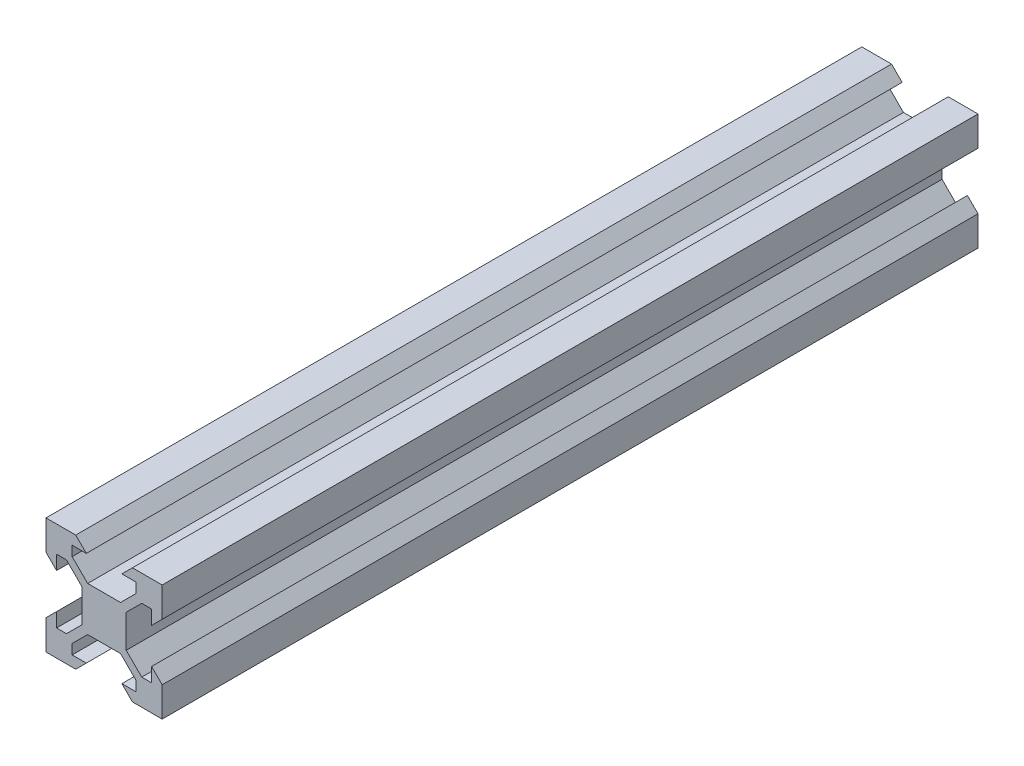
SolidWorks part; units mm, degrees
ref_plane "Front Plane" through (0, 0, 0) normal (0, 0, 1) x (1, 0, 0)
ref_plane "Top Plane" through (0, 0, 0) normal (0, 1, 0) x (1, 0, 0)
ref_plane "Right Plane" through (0, 0, 0) normal (1, 0, 0) x (0, 0, -1)
sketch "Sketch1" plane through (0, 0, 0) normal (0, 0, 1) x (1, 0, 0)
  line L1 (0, 0) -> (20, 0)
  line L2 (0, 0) -> (0, 20)
  line L3 (0, 20) -> (20, 20)
  line L4 (20, 0) -> (20, 20)
  line L5 (0, 0) -> (20, 20) construction
  line L6 (0, 20) -> (20, 0) construction
  point P4 (10, 10)
  dimension "D1" = 20
  dimension "D2" = 20
extrude "Boss-Extrude1" add sketch "Sketch1" along normal blind 140.43
sketch "Sketch2" plane through (0, 0, 140.43) normal (0, 0, 1) x (1, 0, 0)
  line L4 (0, 0) -> (20, 20) construction
  line L5 (4.5, 18.18) -> (6.94, 18.18)
  line L6 (4.5, 16.4758) -> (4.5, 18.18)
  line L15 (7.1658, 13.81) -> (4.5, 16.4758)
  line L17 (12.8342, 13.81) -> (7.1658, 13.81)
  line L27 (15.5, 16.4758) -> (12.8342, 13.81)
  line L29 (15.5, 18.18) -> (15.5, 16.4758)
  line L31 (13.06, 18.18) -> (15.5, 18.18)
  line L33 (14.88, 20) -> (5.12, 20)
  line L35 (6.94, 18.18) -> (5.12, 20)
  line L54 (14.88, 20) -> (13.06, 18.18)
  line L56 (14.88, 0) -> (13.06, 1.82)
  line L57 (6.94, 1.82) -> (5.12, 0)
  line L58 (14.88, 0) -> (5.12, 0)
  line L68 (13.06, 1.82) -> (15.5, 1.82)
  line L71 (15.5, 1.82) -> (15.5, 3.5242)
  line L81 (15.5, 3.5242) -> (12.8342, 6.19)
  line L82 (12.8342, 6.19) -> (7.1658, 6.19)
  line L83 (7.1658, 6.19) -> (4.5, 3.5242)
  line L84 (4.5, 3.5242) -> (4.5, 1.82)
  line L85 (4.5, 1.82) -> (6.94, 1.82)
  line L136 (20, 0) -> (10, 0) construction
  line L137 (0, 0) -> (20, 0) construction
  line L186 (1.82, 4.5) -> (1.82, 6.94)
  line L187 (3.5242, 4.5) -> (1.82, 4.5)
  line L188 (6.19, 7.1658) -> (3.5242, 4.5)
  line L189 (6.19, 12.8342) -> (6.19, 7.1658)
  line L190 (3.5242, 15.5) -> (6.19, 12.8342)
  line L191 (1.82, 15.5) -> (3.5242, 15.5)
  line L192 (1.82, 13.06) -> (1.82, 15.5)
  line L193 (0, 14.88) -> (0, 5.12)
  line L194 (1.82, 6.94) -> (0, 5.12)
  line L195 (0, 14.88) -> (1.82, 13.06)
  line L203 (20, 14.88) -> (18.18, 13.06)
  line L205 (18.18, 6.94) -> (20, 5.12)
  line L206 (20, 14.88) -> (20, 5.12)
  line L207 (18.18, 13.06) -> (18.18, 15.5)
  line L208 (18.18, 15.5) -> (16.4758, 15.5)
  line L209 (16.4758, 15.5) -> (13.81, 12.8342)
  line L210 (13.81, 12.8342) -> (13.81, 7.1658)
  line L211 (13.81, 7.1658) -> (16.4758, 4.5)
  line L212 (16.4758, 4.5) -> (18.18, 4.5)
  line L213 (18.18, 4.5) -> (18.18, 6.94)
extrude "Cut-Extrude1" cut sketch "Sketch2" against normal through all
